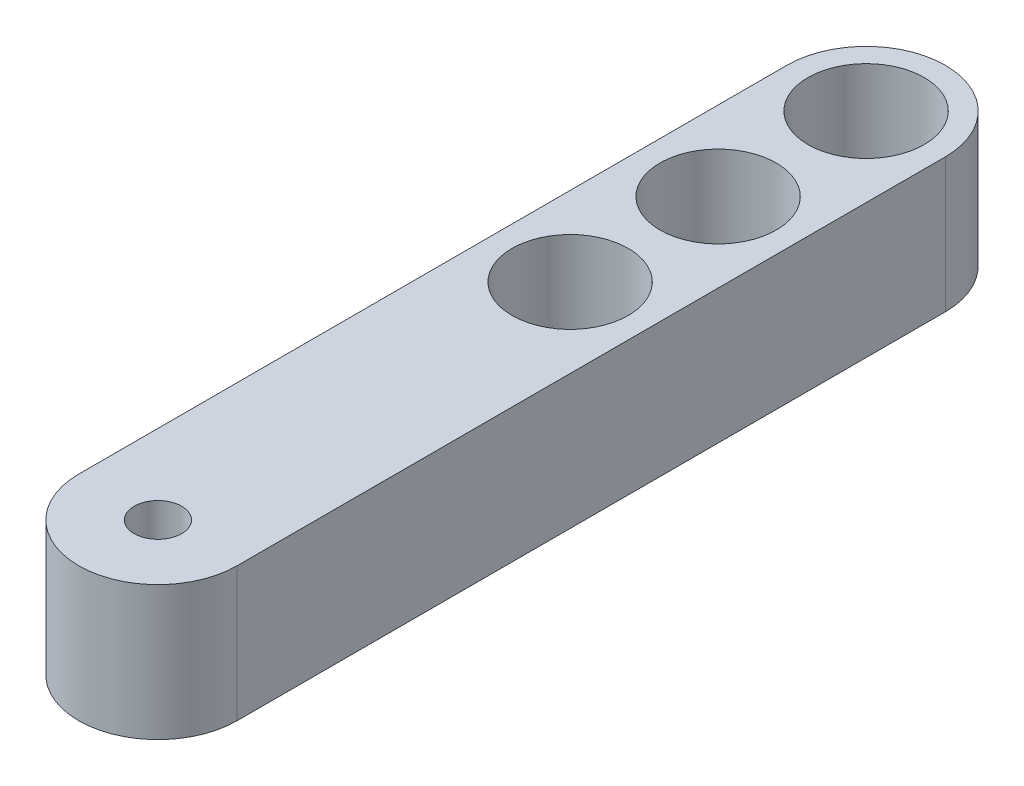
SolidWorks part; units mm, degrees
ref_plane "Front Plane" through (0, 0, 0) normal (0, 0, 1) x (1, 0, 0)
ref_plane "Top Plane" through (0, 0, 0) normal (0, 1, 0) x (1, 0, 0)
ref_plane "Right Plane" through (0, 0, 0) normal (1, 0, 0) x (0, 0, -1)
sketch "Sketch1" plane through (0, 0, 0) normal (0, 1, 0) x (1, 0, 0)
  line L0 (-3.75, 33.5) -> (-3.75, 0)
  line L2 (3.75, 0) -> (3.75, 33.5)
  arc A1 (-3.75, 0) -> (3.75, 0) centre (0, 0) ccw
  arc A2 (3.75, 33.5) -> (-3.75, 33.5) centre (0, 33.5) ccw
  circle A3 centre (0, 0) radius 1.125
  circle A4 centre (0, 33.5) radius 2.75
  dimension "D2" = 3.75
  dimension "D3" = 2.25
  dimension "D4" = 5.5
  dimension "D5" = 3.75
  dimension "D6" = 33.5
  dimension "D1" = 33.5
  dimension "D7" = 33.5
  dimension "D8" = 7.5
extrude "Boss-Extrude1" add sketch "Sketch1" along normal blind 6.35
sketch "Sketch2" plane through (0, 0, 0) normal (0, 1, 0) x (1, 0, 0)
  circle A0 centre (0, 33.5) radius 2.75
  circle A1 centre (0, 19.5) radius 2.75
  circle A2 centre (0, 26.5) radius 2.75
  point P5 (0, 33.5)
  dimension "D1" = 7
  dimension "D2" = 7
extrude "Cut-Extrude2" cut sketch "Sketch2" along normal blind 6.35
